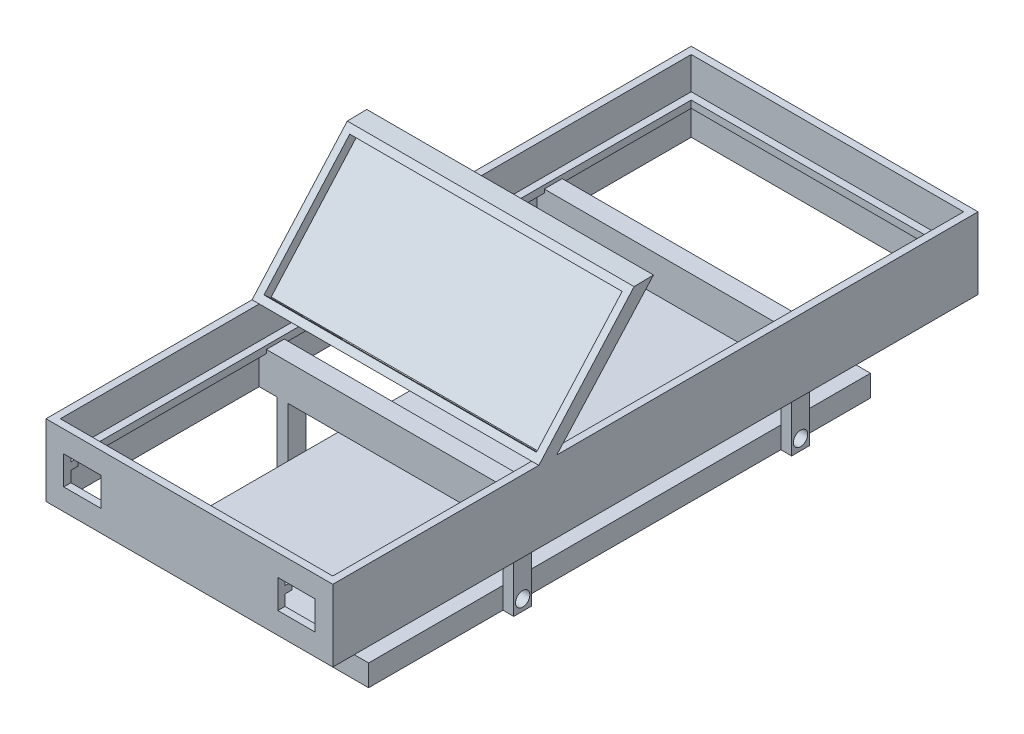
SolidWorks part; units mm, degrees
ref_plane "Front Plane" through (0, 0, 0) normal (0, 0, 1) x (1, 0, 0)
ref_plane "Top Plane" through (0, 0, 0) normal (0, 1, 0) x (1, 0, 0)
ref_plane "Right Plane" through (0, 0, 0) normal (1, 0, 0) x (0, 0, -1)
sketch "Sketch1" plane through (0, 0, 0) normal (0, 0, 1) x (1, 0, 0)
  line L1 (50.8, -25.4) -> (-50.8, -25.4)
  line L2 (50.8, -25.4) -> (50.8, 25.4)
  line L3 (50.8, 25.4) -> (-50.8, 25.4)
  line L4 (-50.8, -25.4) -> (-50.8, 25.4)
  line L5 (50.8, -25.4) -> (-50.8, 25.4) construction
  line L6 (50.8, 25.4) -> (-50.8, -25.4) construction
  point P0 (0, 0)
  dimension "D1" = 101.6
  dimension "D2" = 50.8
extrude "Boss-Extrude1" add sketch "Sketch1" against normal blind 228.6
sketch "Sketch2" plane through (0, 25.4, 0) normal (0, 1, 0) x (1, 0, 0)
  line L0 (0, 0) -> (0, 228.6) construction
  line L1 (50.8, 228.6) -> (-50.8, 228.6) construction
  line L3 (48.26, 200.66) -> (-48.26, 200.66)
  line L4 (48.26, 200.66) -> (48.26, 27.94)
  line L5 (48.26, 27.94) -> (-48.26, 27.94)
  line L6 (-48.26, 200.66) -> (-48.26, 27.94)
  line L7 (48.26, 200.66) -> (-48.26, 27.94) construction
  line L8 (48.26, 27.94) -> (-48.26, 200.66) construction
  point P6 (0, 114.3)
  dimension "D1" = 172.72
  dimension "D2" = 96.52
extrude "Cut-Extrude1" cut sketch "Sketch2" against normal blind 50.8
sketch "Sketch3" plane through (0, 25.4, 0) normal (0, 1, 0) x (1, 0, 0)
  line L0 (0, 0) -> (0, 76.1763)
  line L1 (-48.26, 200.66) -> (-48.26, 27.94) construction
  line L2 (48.26, 79.3513) -> (-48.26, 79.3513)
  line L3 (48.26, 79.3513) -> (48.26, 73.0013)
  line L4 (48.26, 73.0013) -> (-48.26, 73.0013)
  line L5 (-48.26, 79.3513) -> (-48.26, 73.0013)
  line L6 (48.26, 79.3513) -> (-48.26, 73.0013) construction
  line L7 (48.26, 73.0013) -> (-48.26, 79.3513) construction
  dimension "D1" = 6.35
extrude "Boss-Extrude2" add sketch "Sketch3" against normal blind 50.8
sketch "Sketch5" plane through (0, 25.4, 0) normal (0, 1, 0) x (1, 0, 0)
  line L0 (48.26, 73.0013) -> (50.8, 73.0013) construction
  line L3 (50.8, 228.6) -> (50.8, 0) construction
sketch "Sketch6" plane through (50.8, 0, 0) normal (1, 0, 0) x (0, 0, -1)
  line L0 (73.0013, 25.4) -> (106.7566, 63.3634)
  dimension "D1" = 50.8
sketch "Sketch7" plane through (0, 25.4, 0) normal (0, 1, 0) x (1, 0, 0)
  line L0 (48.26, 79.3513) -> (50.8, 79.3513)
  line L1 (50.8, 73.0013) -> (50.8, 106.7566) construction
sketch "Sketch8" plane through (50.8, 0, 0) normal (1, 0, 0) x (0, 0, -1)
  line L0 (79.3513, 25.4) -> (113.6226, 63.5)
  line L2 (106.7566, 63.3634) -> (113.6226, 63.5)
  dimension "D1" = 38.1
sketch "Sketch9" plane through (50.8, 0, 0) normal (1, 0, 0) x (0, 0, -1)
  line L0 (73.0013, 25.4) -> (79.3513, 25.4)
sketch "Sketch10" plane through (0, 25.4, 0) normal (0, 1, 0) x (1, 0, 0)
  line L0 (-48.26, 79.3513) -> (-50.8, 79.3513)
  line L1 (-50.8, 228.6) -> (-50.8, 0) construction
  line L2 (-48.26, 73.0013) -> (-50.8, 73.0013)
sketch "Sketch11" plane through (-50.8, 0, 0) normal (-1, 0, 0) x (0, 0, 1)
  line L0 (-79.3513, 25.4) -> (-113.6226, 63.5)
  line L1 (-73.0013, 25.4) -> (-106.7566, 63.3634)
  line L2 (-106.7566, 63.3634) -> (-113.6226, 63.5)
  line L3 (-79.3513, 25.4) -> (-73.0013, 25.4)
extrude "Boss-Extrude3" add sketch "Sketch11" against normal up to vertex (101.6 mm away) contours L1 L2 L0 L3 up to point (50.8, 63.3634, -106.7566)
sketch "Sketch13" plane through (0, 25.4, 0) normal (0, 1, 0) x (1, 0, 0)
  line L1 (-48.26, 200.66) -> (48.26, 200.66)
  line L2 (-48.26, 200.66) -> (-48.26, 226.06)
  line L3 (-48.26, 226.06) -> (48.26, 226.06)
  line L4 (48.26, 200.66) -> (48.26, 226.06)
  dimension "D1" = 25.4
extrude "Cut-Extrude2" cut sketch "Sketch13" against normal blind 50.8
sketch "Sketch14" plane through (0, 25.4, 0) normal (0, 1, 0) x (1, 0, 0)
  line L1 (-48.26, 27.94) -> (48.26, 27.94)
  line L2 (-48.26, 27.94) -> (-48.26, 2.54)
  line L3 (-48.26, 2.54) -> (48.26, 2.54)
  line L4 (48.26, 27.94) -> (48.26, 2.54)
  dimension "D1" = 96.52
  dimension "D2" = 25.4
extrude "Cut-Extrude3" cut sketch "Sketch14" against normal blind 50.8
sketch "Sketch15" plane through (0, 0, -73.0013) normal (0, 0, 1) x (1, 0, 0)
  line L1 (48.26, -25.4) -> (-48.26, -25.4)
  line L2 (48.26, -25.4) -> (48.26, 25.4)
  line L3 (48.26, 25.4) -> (-48.26, 25.4)
  line L4 (-48.26, -25.4) -> (-48.26, 25.4)
  line L5 (48.26, -25.4) -> (-48.26, 25.4) construction
  line L6 (48.26, 25.4) -> (-48.26, -25.4) construction
  point P0 (0, 0)
  dimension "D1" = 96.52
  dimension "D2" = 50.8
extrude "Cut-Extrude6" cut sketch "Sketch15" against normal blind 6.35
sketch "Sketch16" plane through (0, -25.0354, -28.1564) normal (0, 0.6645, 0.7473) x (1, 0, 0)
  line L0 (0, 67.4892) -> (0, 118.2892) construction
  line L1 (48.26, 67.4892) -> (-48.26, 67.4892) construction
  line L2 (50.8, 118.2892) -> (-50.8, 118.2892) construction
  line L4 (48.26, 70.0292) -> (-48.26, 70.0292)
  line L5 (48.26, 70.0292) -> (48.26, 115.7492)
  line L6 (48.26, 115.7492) -> (-48.26, 115.7492)
  line L7 (-48.26, 70.0292) -> (-48.26, 115.7492)
  line L8 (48.26, 70.0292) -> (-48.26, 115.7492) construction
  line L9 (48.26, 115.7492) -> (-48.26, 70.0292) construction
  point P7 (0, 92.8892)
  dimension "D1" = 96.52
  dimension "D2" = 45.72
extrude "Cut-Extrude7" cut sketch "Sketch16" against normal blind 3.175
sketch "Sketch17" plane through (0, 0, 0) normal (0, 0, 1) x (1, 0, 0)
  line L0 (50.8, 0) -> (-50.8, 0)
  line L1 (-50.8, 25.4) -> (-50.8, -25.4) construction
  line L4 (-50.8, 0) -> (-50.8, -25.4)
  line L5 (-50.8, -25.4) -> (50.8, -25.4)
  line L6 (50.8, 0) -> (50.8, -25.4)
  point P6 (0, 0)
extrude "Cut-Extrude8" cut sketch "Sketch17" against normal blind 228.6
sketch "Sketch18" plane through (48.26, 0, 0) normal (-1, 0, 0) x (0, 0, 1)
  line L0 (-73.0013, 25.4) -> (-73.0013, 0) construction
  line L1 (-228.6, 0) -> (0, 0) construction
  line L2 (-79.3513, 25.4) -> (-79.3513, 0) construction
  line L3 (-79.3513, 0) -> (-73.0013, 0) construction
  line L4 (-73.0013, 12.7) -> (-79.3513, 12.7) construction
sketch "Sketch19" plane through (48.26, 0, 0) normal (-1, 0, 0) x (0, 0, 1)
  line L0 (-73.0013, 12.7) -> (-79.3513, 12.7)
  line L1 (-79.3513, 12.7) -> (-79.3513, 0)
  line L2 (-79.3513, 0) -> (-73.0013, 0)
  line L3 (-73.0013, 12.7) -> (-73.0013, 0)
extrude "Boss-Extrude4" add sketch "Sketch19" along normal blind 96.52
sketch "Sketch20" plane through (-50.8, 0, 0) normal (-1, 0, 0) x (0, 0, 1)
  line L0 (-228.6, 0) -> (-177.8, 0)
  line L1 (-228.6, 0) -> (0, 0) construction
  line L3 (-177.8, 0) -> (-171.45, 0)
  line L4 (-177.8, 0) -> (-177.8, 12.7)
  line L5 (-177.8, 12.7) -> (-171.45, 12.7)
  line L6 (-171.45, 0) -> (-171.45, 12.7)
  line M4 (-228.6, 0) -> (0, 0)
  dimension "D1" = 50.8
  dimension "D2" = 6.35
  dimension "D3" = 12.7
extrude "Boss-Extrude5" add sketch "Sketch20" against normal blind 101.6 contours L6 L5 L4 M4
sketch "Sketch24" plane through (0, 0, 0) normal (0, -1, 0) x (1, 0, 0)
  line L0 (48.26, -79.3513) -> (-48.26, -79.3513) construction
  line L1 (50.8, -73.0013) -> (38.1, -73.0013)
  line L2 (50.8, -73.0013) -> (50.8, -79.3513)
  line L3 (50.8, -79.3513) -> (38.1, -79.3513)
  line L4 (38.1, -73.0013) -> (38.1, -79.3513)
  dimension "D1" = 12.7
extrude "Boss-Extrude8" add sketch "Sketch24" along normal blind 19.05
sketch "Sketch25" plane through (0, 0, 0) normal (0, -1, 0) x (1, 0, 0)
  line L0 (-48.26, -79.3513) -> (38.1, -79.3513) construction
  line L1 (-50.8, -73.0013) -> (-38.1, -73.0013)
  line L2 (-50.8, -73.0013) -> (-50.8, -79.3513)
  line L3 (-50.8, -79.3513) -> (-38.1, -79.3513)
  line L4 (-38.1, -73.0013) -> (-38.1, -79.3513)
  dimension "D1" = 12.7
extrude "Boss-Extrude9" add sketch "Sketch25" along normal blind 19.05
sketch "Sketch26" plane through (0, 0, 0) normal (0, -1, 0) x (1, 0, 0)
  line L0 (-50.8, -228.6) -> (-50.8, -79.3513) construction
  line L1 (-50.8, -171.45) -> (-38.1, -171.45)
  line L2 (-50.8, -171.45) -> (-50.8, -177.8)
  line L3 (-50.8, -177.8) -> (-38.1, -177.8)
  line L4 (-38.1, -171.45) -> (-38.1, -177.8)
  line L5 (48.26, -177.8) -> (-48.26, -177.8) construction
  dimension "D1" = 12.7
extrude "Boss-Extrude10" add sketch "Sketch26" along normal blind 19.05
sketch "Sketch27" plane through (0, 0, 0) normal (0, -1, 0) x (1, 0, 0)
  line L0 (50.8, -228.6) -> (50.8, -79.3513) construction
  line L1 (50.8, -177.8) -> (38.1, -177.8)
  line L2 (50.8, -177.8) -> (50.8, -171.45)
  line L3 (50.8, -171.45) -> (38.1, -171.45)
  line L4 (38.1, -177.8) -> (38.1, -171.45)
  line L5 (48.26, -171.45) -> (-38.1, -171.45) construction
  dimension "D1" = 12.7
extrude "Boss-Extrude11" add sketch "Sketch27" along normal blind 19.05
sketch "Sketch28" plane through (0, 0, -73.0013) normal (0, 0, 1) x (1, 0, 0)
  line L0 (50.8, 0) -> (-50.8, 0) construction
  line L1 (50.8, -19.05) -> (41.91, -19.05)
  line L2 (50.8, -19.05) -> (50.8, 0)
  line L3 (50.8, 0) -> (41.91, 0)
  line L4 (41.91, -19.05) -> (41.91, 0)
  dimension "D1" = 8.89
extrude "Cut-Extrude9" cut sketch "Sketch28" against normal blind 6.35
sketch "Sketch29" plane through (0, 0, -73.0013) normal (0, 0, 1) x (1, 0, 0)
  line L0 (50.8, 0) -> (-50.8, 0) construction
  line L1 (-50.8, -19.05) -> (-41.91, -19.05)
  line L2 (-50.8, -19.05) -> (-50.8, 0)
  line L3 (-50.8, 0) -> (-41.91, 0)
  line L4 (-41.91, -19.05) -> (-41.91, 0)
  dimension "D1" = 8.89
extrude "Cut-Extrude10" cut sketch "Sketch29" against normal blind 6.35
sketch "Sketch30" plane through (0, 0, -171.45) normal (0, 0, 1) x (1, 0, 0)
  line L1 (-50.8, -19.05) -> (-41.91, -19.05)
  line L2 (-50.8, -19.05) -> (-50.8, 0)
  line L3 (-50.8, 0) -> (-41.91, 0)
  line L4 (-41.91, -19.05) -> (-41.91, 0)
extrude "Cut-Extrude11" cut sketch "Sketch30" against normal blind 6.35
sketch "Sketch31" plane through (0, 0, -171.45) normal (0, 0, 1) x (1, 0, 0)
  line L0 (41.91, 0) -> (41.91, -19.05) construction
  line L1 (50.8, -19.05) -> (41.91, -19.05)
  line L2 (50.8, -19.05) -> (50.8, 0)
  line L3 (50.8, 0) -> (41.91, 0)
  line L4 (41.91, -19.05) -> (41.91, 0)
extrude "Cut-Extrude12" cut sketch "Sketch31" against normal blind 6.35
sketch "Sketch33" plane through (0, 0, -2.54) normal (0, 0, -1) x (-1, 0, 0)
  line L1 (48.26, 0) -> (48.26, 25.4) construction
  line L2 (48.26, 12.7) -> (-48.26, 12.7) construction
  line L3 (-48.26, 0) -> (-48.26, 25.4) construction
  line L5 (48.26, 13.97) -> (-48.26, 13.97)
  line L6 (48.26, 13.97) -> (48.26, 11.43)
  line L7 (48.26, 11.43) -> (-48.26, 11.43)
  line L8 (-48.26, 13.97) -> (-48.26, 11.43)
  line L9 (48.26, 13.97) -> (-48.26, 11.43) construction
  line L10 (48.26, 11.43) -> (-48.26, 13.97) construction
  point P6 (0, 12.7)
  dimension "D1" = 2.54
extrude "Boss-Extrude13" add sketch "Sketch33" along normal blind 2.54
sketch "Sketch34" plane through (0, 0, -226.06) normal (0, 0, 1) x (1, 0, 0)
  line L0 (0, 0) -> (0, 25.4) construction
  line L1 (-48.26, 0) -> (-48.26, 25.4) construction
  line L2 (48.26, 12.7) -> (-48.26, 12.7) construction
  line L3 (48.26, 0) -> (48.26, 25.4) construction
  line L4 (-48.26, 0) -> (48.26, 0) construction
  line L5 (48.26, 25.4) -> (-48.26, 25.4) construction
  line L7 (48.26, 13.97) -> (-48.26, 13.97)
  line L8 (48.26, 13.97) -> (48.26, 11.43)
  line L9 (48.26, 11.43) -> (-48.26, 11.43)
  line L10 (-48.26, 13.97) -> (-48.26, 11.43)
  line L11 (48.26, 13.97) -> (-48.26, 11.43) construction
  line L12 (48.26, 11.43) -> (-48.26, 13.97) construction
  point P12 (0, 12.7)
  dimension "D1" = 2.54
extrude "Boss-Extrude17" add sketch "Sketch34" along normal blind 2.54
sketch "Sketch36" plane through (-48.26, 0, 0) normal (1, 0, 0) x (0, 0, -1)
  line L0 (5.08, 11.43) -> (5.08, 13.97) construction
  line L1 (5.08, 13.97) -> (223.52, 13.97)
  line L2 (5.08, 13.97) -> (5.08, 11.43)
  line L3 (5.08, 11.43) -> (223.52, 11.43)
  line L4 (223.52, 13.97) -> (223.52, 11.43)
extrude "Boss-Extrude18" add sketch "Sketch36" along normal blind 2.54
sketch "Sketch37" plane through (48.26, 0, 0) normal (-1, 0, 0) x (0, 0, 1)
  line L1 (-5.08, 13.97) -> (-223.52, 13.97)
  line L2 (-5.08, 13.97) -> (-5.08, 11.43)
  line L3 (-5.08, 11.43) -> (-223.52, 11.43)
  line L4 (-223.52, 13.97) -> (-223.52, 11.43)
extrude "Boss-Extrude19" add sketch "Sketch37" along normal blind 2.54
sketch "Sketch42" plane through (-41.91, 0, 0) normal (-1, 0, 0) x (0, 0, 1)
  line L0 (-73.0013, -19.05) -> (-73.0013, 0) construction
  line L1 (-73.0013, -12.7) -> (-79.3513, -12.7)
  line L2 (-73.0013, -12.7) -> (-73.0013, -19.05)
  line L3 (-73.0013, -19.05) -> (-79.3513, -19.05)
  line L4 (-79.3513, -12.7) -> (-79.3513, -19.05)
  line L5 (-79.3513, -19.05) -> (-79.3513, 0) construction
extrude "Cut-Extrude16" cut sketch "Sketch42" against normal blind 5.08
sketch "Sketch45" plane through (0, 0, 0) normal (0, 0, 1) x (1, 0, 0)
  line L0 (-50.8, 12.7) -> (50.8, 12.7) construction
  line L1 (-50.8, 25.4) -> (-50.8, 0) construction
  line L2 (50.8, 0) -> (50.8, 25.4) construction
  line L3 (0, 0) -> (0, 25.4) construction
  line L4 (48.26, 25.4) -> (-48.26, 25.4) construction
  line L5 (0, 12.7) -> (-50.8, 12.7) construction
  line L6 (-25.0661, 12.7) -> (-50.8, 12.7) construction
  line L7 (44.537, 17.78) -> (44.537, 7.62)
  line L8 (-31.329, 17.78) -> (-44.537, 17.78)
  line L9 (-31.329, 17.78) -> (-31.329, 7.62)
  line L10 (-31.329, 7.62) -> (-44.537, 7.62)
  line L11 (-44.537, 17.78) -> (-44.537, 7.62)
  line L12 (-31.329, 17.78) -> (-44.537, 7.62) construction
  line L13 (-31.329, 7.62) -> (-44.537, 17.78) construction
  line L14 (31.329, 7.62) -> (44.537, 7.62)
  line L15 (31.329, 17.78) -> (31.329, 7.62)
  line L16 (31.329, 17.78) -> (44.537, 17.78)
  point P13 (-37.933, 12.7)
  dimension "D1" = 13.208
  dimension "D2" = 10.16
extrude "Cut-Extrude19" cut sketch "Sketch45" against normal blind 6.35
sketch "Sketch50" plane through (-41.91, 0, 0) normal (-1, 0, 0) x (0, 0, 1)
  line L0 (-79.3513, -12.7) -> (-79.3513, -19.05)
  line L1 (-73.0013, -12.7) -> (-73.0013, -19.05)
  line L2 (-79.3513, -19.05) -> (-73.0013, -19.05)
  line L7 (-79.3513, 0) -> (-79.3513, -12.7)
  line L8 (-79.3513, -12.7) -> (-73.0013, -12.7)
  line L9 (-73.0013, -12.7) -> (-73.0013, 0)
  line L10 (-73.0013, 0) -> (-79.3513, 0)
  line L12 (-79.3513, -12.7) -> (-73.0013, -12.7)
  dimension "D1" = 6.35
  dimension "D2" = 0
extrude "Boss-Extrude20" add sketch "Sketch50" against normal blind 3.81 contours L0 L2 L1 L12
sketch "Sketch51" plane through (-41.91, 0, 0) normal (-1, 0, 0) x (0, 0, 1)
  line L0 (-79.3513, -19.05) -> (-79.3513, -25.4)
  line L1 (-73.0013, -19.05) -> (-73.0013, -25.4)
  line L2 (-73.0013, -25.4) -> (-79.3513, -25.4)
  line L7 (-79.3513, 0) -> (-79.3513, -19.05)
  line L8 (-79.3513, -19.05) -> (-73.0013, -19.05)
  line L9 (-73.0013, -19.05) -> (-73.0013, 0)
  line L10 (-73.0013, 0) -> (-79.3513, 0)
  line L12 (-79.3513, -19.05) -> (-73.0013, -19.05)
  dimension "D1" = 6.35
  dimension "D2" = 0
extrude "Boss-Extrude21" add sketch "Sketch51" against normal blind 3.81
sketch "Sketch52" plane through (-41.91, 0, 0) normal (-1, 0, 0) x (0, 0, 1)
  line L0 (-177.8, -19.05) -> (-177.8, -25.4)
  line L1 (-171.45, -19.05) -> (-171.45, -25.4)
  line L2 (-171.45, -25.4) -> (-177.8, -25.4)
  line L7 (-171.45, -19.05) -> (-171.45, 0)
  line L8 (-171.45, 0) -> (-177.8, 0)
  line L9 (-177.8, 0) -> (-177.8, -19.05)
  line L10 (-177.8, -19.05) -> (-171.45, -19.05)
  line L14 (-177.8, -19.05) -> (-171.45, -19.05)
  dimension "D1" = 6.35
  dimension "D2" = 0
extrude "Boss-Extrude22" add sketch "Sketch52" against normal blind 3.81
sketch "Sketch53" plane through (41.91, 0, 0) normal (1, 0, 0) x (0, 0, -1)
  line L0 (73.0013, -19.05) -> (73.0013, -25.4)
  line L1 (79.3513, -25.4) -> (79.3513, -19.05)
  line L2 (79.3513, -25.4) -> (79.3513, 0) construction
  line L3 (79.3513, 0) -> (79.3513, -19.05) construction
  line L4 (73.0013, -25.4) -> (79.3513, -25.4)
  line L5 (73.0013, -19.05) -> (79.3513, -19.05)
extrude "Boss-Extrude23" add sketch "Sketch53" against normal blind 3.81
sketch "Sketch54" plane through (41.91, 0, 0) normal (1, 0, 0) x (0, 0, -1)
  line L0 (171.45, -19.05) -> (171.45, -25.4)
  line L1 (177.8, -25.4) -> (171.45, -25.4) construction
  line L2 (171.45, -25.4) -> (171.45, 0) construction
  line L3 (171.45, -25.4) -> (177.8, -25.4)
  line L4 (177.8, -25.4) -> (177.8, -19.05)
  line L5 (177.8, -19.05) -> (171.45, -19.05)
extrude "Boss-Extrude24" add sketch "Sketch54" against normal blind 3.81
sketch "Sketch55" plane through (0, -25.4, 0) normal (0, -1, 0) x (1, 0, 0)
  line L0 (0, -226.06) -> (0, -2.54) construction
  line L1 (-48.26, -226.06) -> (48.26, -226.06) construction
  line L2 (48.26, -2.54) -> (-48.26, -2.54) construction
  line L4 (38.1, -25.4) -> (-38.1, -25.4)
  line L5 (38.1, -25.4) -> (38.1, -203.2)
  line L6 (38.1, -203.2) -> (-38.1, -203.2)
  line L7 (-38.1, -25.4) -> (-38.1, -203.2)
  line L8 (38.1, -25.4) -> (-38.1, -203.2) construction
  line L9 (38.1, -203.2) -> (-38.1, -25.4) construction
  point P6 (0, -114.3)
  dimension "D1" = 177.8
  dimension "D2" = 76.2
extrude "Boss-Extrude25" add sketch "Sketch55" against normal blind 7.62
sketch "Sketch56" plane through (-41.91, 0, 0) normal (-1, 0, 0) x (0, 0, 1)
  line L0 (-79.3513, -21.59) -> (-73.0013, -21.59) construction
  line L1 (-79.3513, -25.4) -> (-79.3513, -17.78) construction
  line L2 (-73.0013, -25.4) -> (-73.0013, -17.78) construction
  circle A0 centre (-76.1763, -21.59) radius 2.54
  dimension "D1" = 5.08
extrude "Cut-Extrude20" cut sketch "Sketch56" against normal blind 83.82
sketch "Sketch57" plane through (-41.91, 0, 0) normal (-1, 0, 0) x (0, 0, 1)
  line L0 (-177.8, -21.59) -> (-171.45, -21.59) construction
  line L1 (-177.8, -25.4) -> (-177.8, -17.78) construction
  line L2 (-171.45, -25.4) -> (-171.45, 0) construction
  circle A0 centre (-174.625, -21.59) radius 2.54
  dimension "D1" = 5.08
extrude "Cut-Extrude21" cut sketch "Sketch57" against normal blind 83.82
